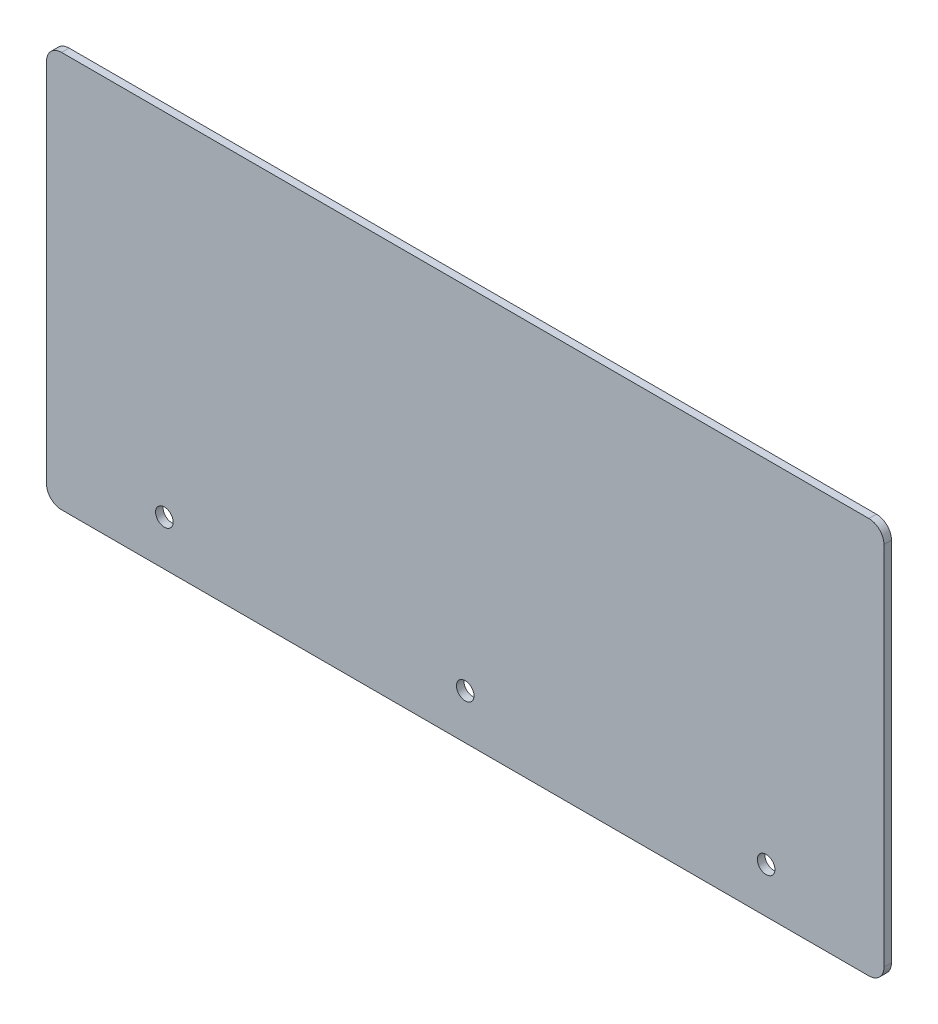
SolidWorks part; units mm, degrees
material "1023 Tôle d'acier au carbone (SS)"
ref_plane "Front" through (0, 0, 0) normal (0, 0, 1) x (1, 0, 0)
ref_plane "Top" through (0, 0, 0) normal (0, 1, 0) x (1, 0, 0)
ref_plane "Right" through (0, 0, 0) normal (1, 0, 0) x (0, 0, -1)
sketch "Esquisse1" plane through (0, 0, 0) normal (0, 0, 1) x (1, 0, 0)
  line L1 (0, 0) -> (167, 0)
  line L2 (0, 0) -> (0, 79)
  line L3 (0, 79) -> (167, 79)
  line L4 (167, 0) -> (167, 79)
  dimension "D1" = 167
  dimension "D2" = 79
extrude "Boss.-Extru.1" add sketch "Esquisse1" along normal blind 1.5
fillet "Congé1" radius 3 4 edges at (167, 0, 0.75) (167, 79, 0.75) (0, 79, 0.75) (0, 0, 0.75)
sketch "Esquisse2" plane through (0, 0, 1.5) normal (0, 0, 1) x (1, 0, 0)
  line L0 (83.5, 79) -> (83.5, 0) construction
  line L1 (164, 79) -> (3, 79) construction
  line L2 (3, 0) -> (164, 0) construction
  line L3 (23.5, 9) -> (83.5, 9) construction
  circle A0 centre (23.5, 9) radius 1.75
  circle A1 centre (83.5, 9) radius 1.75
  circle A2 centre (143.5, 9) radius 1.75
  point P10 (83.5, 9)
  dimension "D2" = 3.5
  dimension "D3" = 9
  dimension "D4" = 60
extrude "Enlèv. mat.-Extru.1" cut sketch "Esquisse2" against normal through all both and the other way through all
